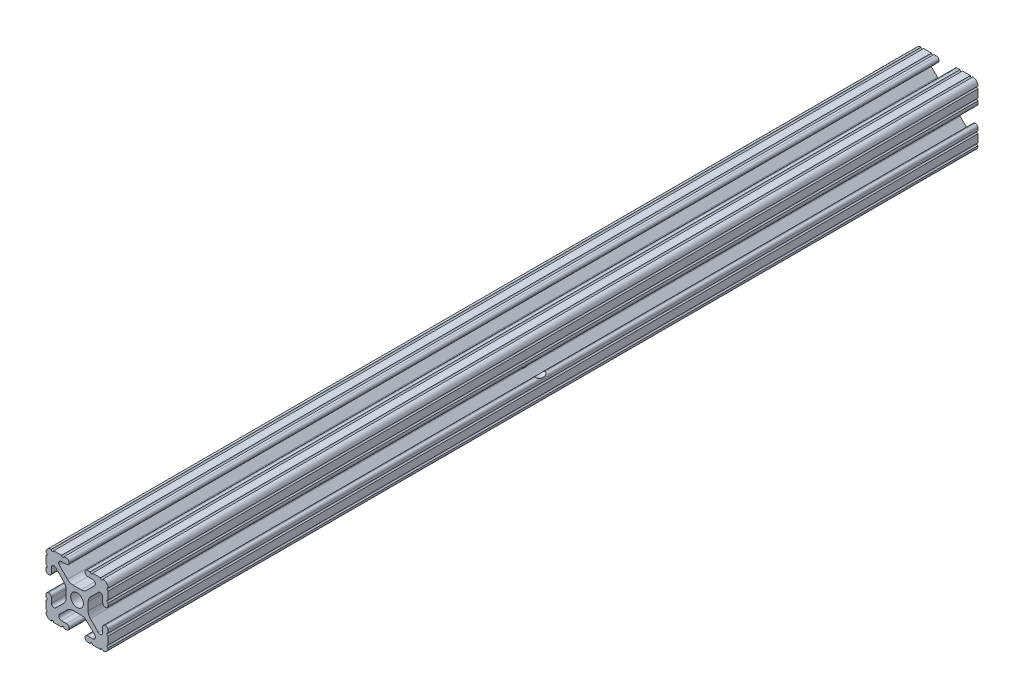
SolidWorks part; units mm, degrees
ref_plane "Front Plane" through (0, 0, 0) normal (0, 0, 1) x (1, 0, 0)
ref_plane "Top Plane" through (0, 0, 0) normal (0, 1, 0) x (1, 0, 0)
ref_plane "Right Plane" through (0, 0, 0) normal (1, 0, 0) x (0, 0, -1)
sketch "Sketch1" plane through (0, 0, 0) normal (0, 0, 1) x (1, 0, 0)
  line L88 (-7.1797, -8.6452) -> (-3.9523, -5.4237)
  line L89 (-1.7093, -4.4958) -> (1.7093, -4.4958)
  line L90 (3.9523, -5.4237) -> (7.1797, -8.6452)
  line L91 (6.4164, -10.4902) -> (4.2875, -10.4902)
  line L92 (3.2385, -11.5392) -> (3.2385, -11.651)
  line L93 (4.2875, -12.7) -> (5.3171, -12.7)
  line L94 (6.3331, -12.7) -> (9.5504, -12.7)
  line L95 (12.7, -9.5504) -> (12.7, -6.3331)
  line L96 (12.7, -5.3171) -> (12.7, -4.2875)
  line L97 (11.651, -3.2385) -> (11.5392, -3.2385)
  line L98 (10.4902, -4.2875) -> (10.4902, -6.4021)
  line L99 (8.7371, -7.1294) -> (5.441, -3.8408)
  line L100 (4.5085, -1.5932) -> (4.5085, 1.5932)
  line L101 (5.441, 3.8408) -> (8.7371, 7.1294)
  line L102 (10.4902, 6.4021) -> (10.4902, 4.2875)
  line L103 (11.5392, 3.2385) -> (11.651, 3.2385)
  line L104 (12.7, 4.2875) -> (12.7, 5.3171)
  line L105 (12.7, 6.3331) -> (12.7, 9.5504)
  line L106 (9.5504, 12.7) -> (6.3331, 12.7)
  line L107 (5.3171, 12.7) -> (4.2875, 12.7)
  line L108 (3.2385, 11.651) -> (3.2385, 11.5392)
  line L109 (4.2875, 10.4902) -> (6.4768, 10.4902)
  line L110 (7.207, 8.7244) -> (3.8983, 5.4232)
  line L111 (1.6558, 4.4958) -> (-1.6558, 4.4958)
  line L112 (-3.8983, 5.4232) -> (-7.207, 8.7244)
  line L113 (-6.4768, 10.4902) -> (-4.2875, 10.4902)
  line L114 (-3.2385, 11.5392) -> (-3.2385, 11.651)
  line L115 (-4.2875, 12.7) -> (-5.3171, 12.7)
  line L116 (-6.3331, 12.7) -> (-9.5504, 12.7)
  line L117 (-12.7, 9.5504) -> (-12.7, 6.3331)
  line L118 (-12.7, 5.3171) -> (-12.7, 4.2875)
  line L119 (-11.651, 3.2385) -> (-11.5392, 3.2385)
  line L120 (-10.4902, 4.2875) -> (-10.4902, 6.4021)
  line L121 (-8.7371, 7.1294) -> (-5.441, 3.8408)
  line L122 (-4.5085, 1.5932) -> (-4.5085, -1.5932)
  line L123 (-5.441, -3.8408) -> (-8.7371, -7.1294)
  line L124 (-10.4902, -6.4021) -> (-10.4902, -4.2875)
  line L125 (-11.5392, -3.2385) -> (-11.651, -3.2385)
  line L126 (-12.7, -4.2875) -> (-12.7, -5.3171)
  line L127 (-12.7, -6.3331) -> (-12.7, -9.5504)
  line L128 (-9.5504, -12.7) -> (-6.3331, -12.7)
  line L129 (-5.3171, -12.7) -> (-4.2875, -12.7)
  line L130 (-3.2385, -11.651) -> (-3.2385, -11.5392)
  line L131 (-4.2875, -10.4902) -> (-6.4164, -10.4902)
  circle A1 centre (0, 0) radius 2.6035
  arc A104 (-7.1797, -8.6452) -> (-6.4164, -10.4902) centre (-6.4164, -9.4098) ccw
  arc A105 (-1.7093, -4.4958) -> (-3.9523, -5.4237) centre (-1.7093, -7.6708) ccw
  arc A106 (3.9523, -5.4237) -> (1.7093, -4.4958) centre (1.7093, -7.6708) ccw
  arc A107 (6.4164, -10.4902) -> (7.1797, -8.6452) centre (6.4164, -9.4098) ccw
  arc A108 (4.2875, -10.4902) -> (3.2385, -11.5392) centre (4.2875, -11.5392) ccw
  arc A109 (3.2385, -11.651) -> (4.2875, -12.7) centre (4.2875, -11.651) ccw
  arc A110 (6.3331, -12.7) -> (5.3171, -12.7) centre (5.8251, -12.7) ccw
  arc A111 (10.5664, -12.6998) -> (9.5504, -12.7) centre (10.0584, -12.7) ccw
  arc A112 (10.5664, -12.6998) -> (12.6998, -10.5664) centre (10.5918, -10.5918) ccw
  arc A113 (12.7, -9.5504) -> (12.6998, -10.5664) centre (12.7, -10.0584) ccw
  arc A114 (12.7, -5.3171) -> (12.7, -6.3331) centre (12.7, -5.8251) ccw
  arc A115 (12.7, -4.2875) -> (11.651, -3.2385) centre (11.651, -4.2875) ccw
  arc A116 (11.5392, -3.2385) -> (10.4902, -4.2875) centre (11.5392, -4.2875) ccw
  arc A117 (8.7371, -7.1294) -> (10.4902, -6.4021) centre (9.4628, -6.4021) ccw
  arc A118 (4.5085, -1.5932) -> (5.441, -3.8408) centre (7.6835, -1.5932) ccw
  arc A119 (5.441, 3.8408) -> (4.5085, 1.5932) centre (7.6835, 1.5932) ccw
  arc A120 (10.4902, 6.4021) -> (8.7371, 7.1294) centre (9.4628, 6.4021) ccw
  arc A121 (10.4902, 4.2875) -> (11.5392, 3.2385) centre (11.5392, 4.2875) ccw
  arc A122 (11.651, 3.2385) -> (12.7, 4.2875) centre (11.651, 4.2875) ccw
  arc A123 (12.7, 6.3331) -> (12.7, 5.3171) centre (12.7, 5.8251) ccw
  arc A124 (12.6998, 10.5664) -> (12.7, 9.5504) centre (12.7, 10.0584) ccw
  arc A125 (12.6998, 10.5664) -> (10.5664, 12.6998) centre (10.5918, 10.5918) ccw
  arc A126 (9.5504, 12.7) -> (10.5664, 12.6998) centre (10.0584, 12.7) ccw
  arc A127 (5.3171, 12.7) -> (6.3331, 12.7) centre (5.8251, 12.7) ccw
  arc A128 (4.2875, 12.7) -> (3.2385, 11.651) centre (4.2875, 11.651) ccw
  arc A129 (3.2385, 11.5392) -> (4.2875, 10.4902) centre (4.2875, 11.5392) ccw
  arc A130 (7.207, 8.7244) -> (6.4768, 10.4902) centre (6.4768, 9.4563) ccw
  arc A131 (1.6558, 4.4958) -> (3.8983, 5.4232) centre (1.6558, 7.6708) ccw
  arc A132 (-3.8983, 5.4232) -> (-1.6558, 4.4958) centre (-1.6558, 7.6708) ccw
  arc A133 (-6.4768, 10.4902) -> (-7.207, 8.7244) centre (-6.4768, 9.4563) ccw
  arc A134 (-4.2875, 10.4902) -> (-3.2385, 11.5392) centre (-4.2875, 11.5392) ccw
  arc A135 (-3.2385, 11.651) -> (-4.2875, 12.7) centre (-4.2875, 11.651) ccw
  arc A136 (-6.3331, 12.7) -> (-5.3171, 12.7) centre (-5.8251, 12.7) ccw
  arc A137 (-10.5664, 12.6998) -> (-9.5504, 12.7) centre (-10.0584, 12.7) ccw
  arc A138 (-10.5664, 12.6998) -> (-12.6998, 10.5664) centre (-10.5918, 10.5918) ccw
  arc A139 (-12.7, 9.5504) -> (-12.6998, 10.5664) centre (-12.7, 10.0584) ccw
  arc A140 (-12.7, 5.3171) -> (-12.7, 6.3331) centre (-12.7, 5.8251) ccw
  arc A141 (-12.7, 4.2875) -> (-11.651, 3.2385) centre (-11.651, 4.2875) ccw
  arc A142 (-11.5392, 3.2385) -> (-10.4902, 4.2875) centre (-11.5392, 4.2875) ccw
  arc A143 (-8.7371, 7.1294) -> (-10.4902, 6.4021) centre (-9.4628, 6.4021) ccw
  arc A144 (-4.5085, 1.5932) -> (-5.441, 3.8408) centre (-7.6835, 1.5932) ccw
  arc A145 (-5.441, -3.8408) -> (-4.5085, -1.5932) centre (-7.6835, -1.5932) ccw
  arc A146 (-10.4902, -6.4021) -> (-8.7371, -7.1294) centre (-9.4628, -6.4021) ccw
  arc A147 (-10.4902, -4.2875) -> (-11.5392, -3.2385) centre (-11.5392, -4.2875) ccw
  arc A148 (-11.651, -3.2385) -> (-12.7, -4.2875) centre (-11.651, -4.2875) ccw
  arc A149 (-12.7, -6.3331) -> (-12.7, -5.3171) centre (-12.7, -5.8251) ccw
  arc A150 (-12.6998, -10.5664) -> (-12.7, -9.5504) centre (-12.7, -10.0584) ccw
  arc A151 (-12.6998, -10.5664) -> (-10.5664, -12.6998) centre (-10.5918, -10.5918) ccw
  arc A152 (-9.5504, -12.7) -> (-10.5664, -12.6998) centre (-10.0584, -12.7) ccw
  arc A153 (-5.3171, -12.7) -> (-6.3331, -12.7) centre (-5.8251, -12.7) ccw
  arc A154 (-4.2875, -12.7) -> (-3.2385, -11.651) centre (-4.2875, -11.651) ccw
  arc A155 (-3.2385, -11.5392) -> (-4.2875, -10.4902) centre (-4.2875, -11.5392) ccw
extrude "Boss-Extrude1" add sketch "Sketch1" along normal mid plane 355.6
sketch "Sketch2" plane through (-12.7, 0, 0) normal (-1, 0, 0) x (0, 0, 1)
  circle A0 centre (0, 0) radius 3.81
  dimension "D1" = 7.62
extrude "Cut-Extrude1" cut sketch "Sketch2" against normal blind 25.4
